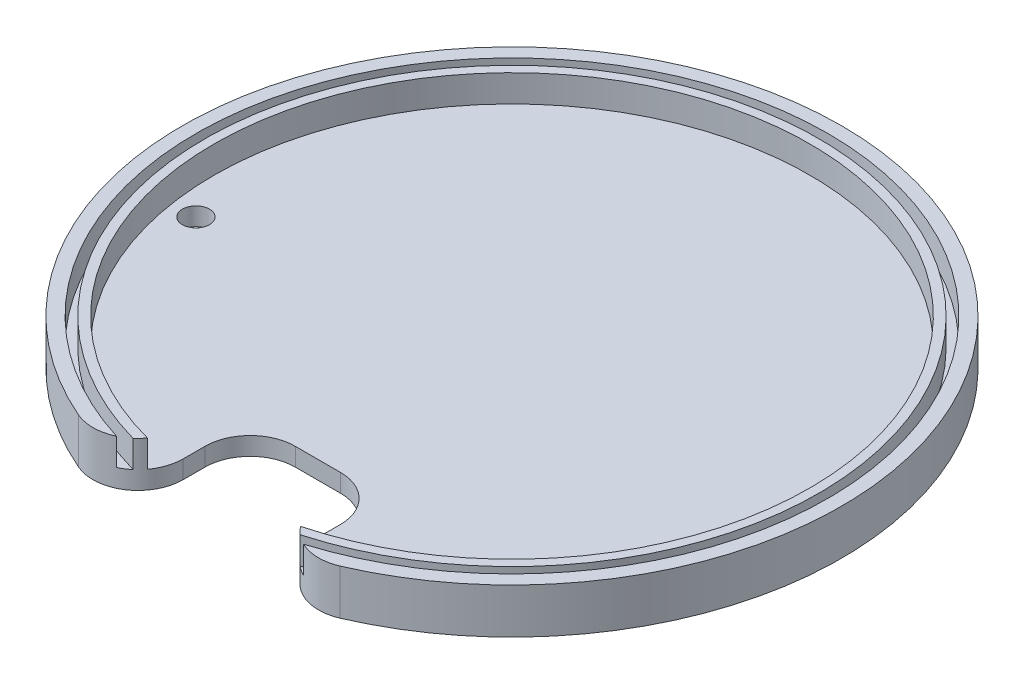
SolidWorks part; units mm, degrees
ref_plane "Front Plane" through (0, 0, 0) normal (0, 0, 1) x (1, 0, 0)
ref_plane "Top Plane" through (0, 0, 0) normal (0, 1, 0) x (1, 0, 0)
ref_plane "Right Plane" through (0, 0, 0) normal (1, 0, 0) x (0, 0, -1)
sketch "Sketch1" plane through (0, 0, 0) normal (0, 1, 0) x (1, 0, 0)
  circle A0 centre (0, 0) radius 73
  dimension "D1" = 146
extrude "Boss-Extrude1" add sketch "Sketch1" along normal blind 4
sketch "Sketch2" plane through (0, 4, 0) normal (0, 1, 0) x (1, 0, 0)
  circle A0 centre (0, 0) radius 73
  circle A1 centre (0, 0) radius 70
  circle A2 centre (0, 0) radius 68
  circle A3 centre (0, 0) radius 66
  circle A4 centre (0, 0) radius 73 construction
  circle M4 centre (0, 0) radius 73
  dimension "D1" = 140
  dimension "D2" = 136
  dimension "D3" = 132
extrude "Boss-Extrude2" add sketch "Sketch2" along normal blind 6 contours A2 A3 | A1 M4
sketch "Sketch4" plane through (0, 0, 0) normal (0, -1, 0) x (1, 0, 0)
  line L0 (0, 0) -> (0, 73) construction
  line L2 (-15, 73) -> (15, 73)
  line L3 (-15, 73) -> (-15, 43)
  line L4 (-15, 43) -> (15, 43)
  line L5 (15, 73) -> (15, 43)
  circle A0 centre (0, 0) radius 73 construction
  dimension "D1" = 30
  dimension "D2" = 15
  dimension "D3" = 15
extrude "Cut-Extrude1" cut sketch "Sketch4" against normal up to next
fillet "Fillet1" radius 10 2 edges at (15, 5, 71.4423) (-15, 5, 71.4423)
fillet "Fillet2" radius 10 2 edges at (15, 2, 43) (-15, 2, 43)
sketch "Sketch6" plane through (0, 0, 0) normal (0, -1, 0) x (1, 0, 0)
  line L0 (0, 0) -> (0, 43) construction
  line L1 (-5, 43) -> (5, 43) construction
  line L2 (0, 0) -> (-73, 0) construction
  circle A0 centre (-60, 10) radius 3
  arc A1 (-28.9683, 67.0063) -> (28.9683, 67.0063) centre (0, 0) ccw construction
  dimension "D1" = 6
  dimension "D2" = 60
  dimension "D3" = 10
extrude "Cut-Extrude2" cut sketch "Sketch6" against normal up to next
